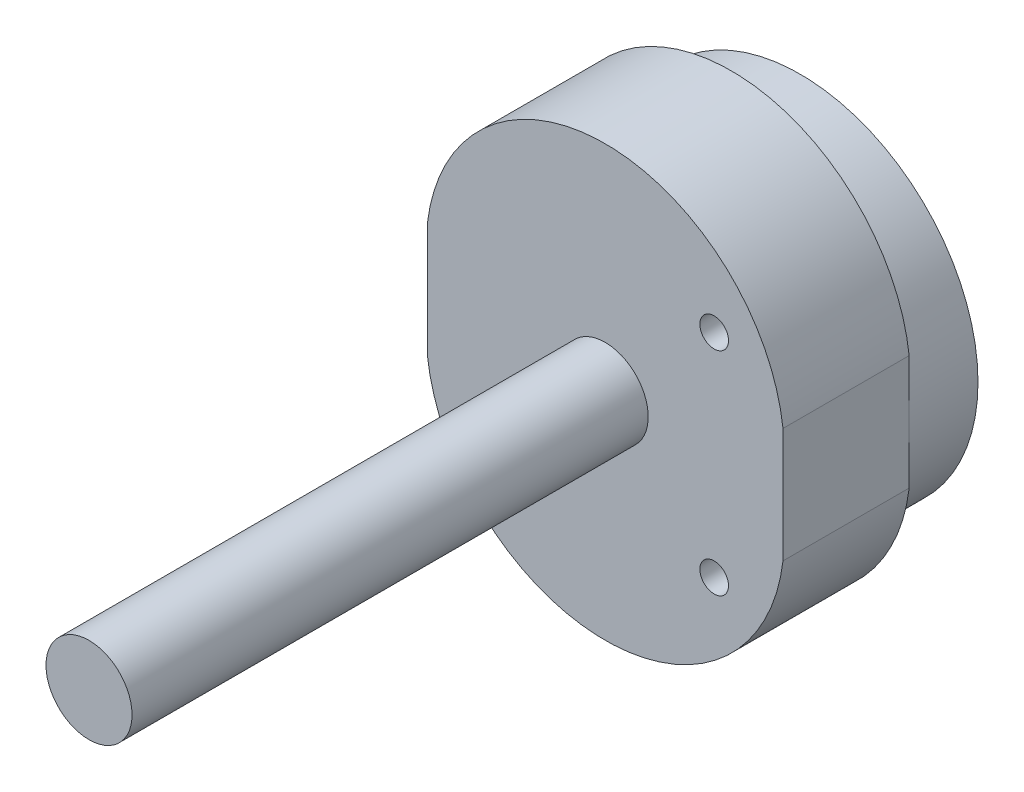
SolidWorks part; units mm, degrees
ref_plane "Front Plane" through (0, 0, 0) normal (0, 0, 1) x (1, 0, 0)
ref_plane "Top Plane" through (0, 0, 0) normal (0, 1, 0) x (1, 0, 0)
ref_plane "Right Plane" through (0, 0, 0) normal (1, 0, 0) x (0, 0, -1)
sketch "Sketch1" plane through (0, 0, 0) normal (0, 0, 1) x (1, 0, 0)
  line L2 (-31, -10) -> (-31, 10)
  line L4 (31, -10) -> (31, 10)
  line L5 (-22.8122, -27.5954) -> (22.8122, 27.5954) construction
  line L6 (-22.8122, 27.5954) -> (22.8122, -27.5954) construction
  arc A0 (-31, 10) -> (31, 10) centre (0, 6.2773) cw
  arc A1 (-31, -10) -> (31, -10) centre (0, -6.2773) ccw
  point P0 (0, 0)
  point P2 (0, 37.5)
  point P18 (0, -37.5)
  dimension "D3" = 10
  dimension "D4" = 10
  dimension "D1" = 62
  dimension "D2" = 75
extrude "Boss-Extrude1" add sketch "Sketch1" along normal blind 22
sketch "Sketch2" plane through (0, 0, 0) normal (0, 0, -1) x (-1, 0, 0)
  circle A0 centre (0, 0) radius 31
  dimension "D1" = 62
extrude "Boss-Extrude2" add sketch "Sketch2" along normal blind 12
sketch "Sketch3" plane through (0, 0, 22) normal (0, 0, 1) x (1, 0, 0)
  line L0 (31, -10) -> (31, 10) construction
  circle A0 centre (19, 18.5) radius 2.5
  circle A1 centre (19, -18.5) radius 2.5
  dimension "D1" = 5
  dimension "D2" = 5
  dimension "D3" = 37
  dimension "D4" = 18.5
  dimension "D5" = 12
extrude "Cut-Extrude2" cut sketch "Sketch3" against normal blind 12
sketch "Sketch4" plane through (0, 0, 22) normal (0, 0, 1) x (1, 0, 0)
  circle A0 centre (0, 0) radius 7.5
  dimension "D1" = 15
extrude "Boss-Extrude3" add sketch "Sketch4" along normal blind 90
